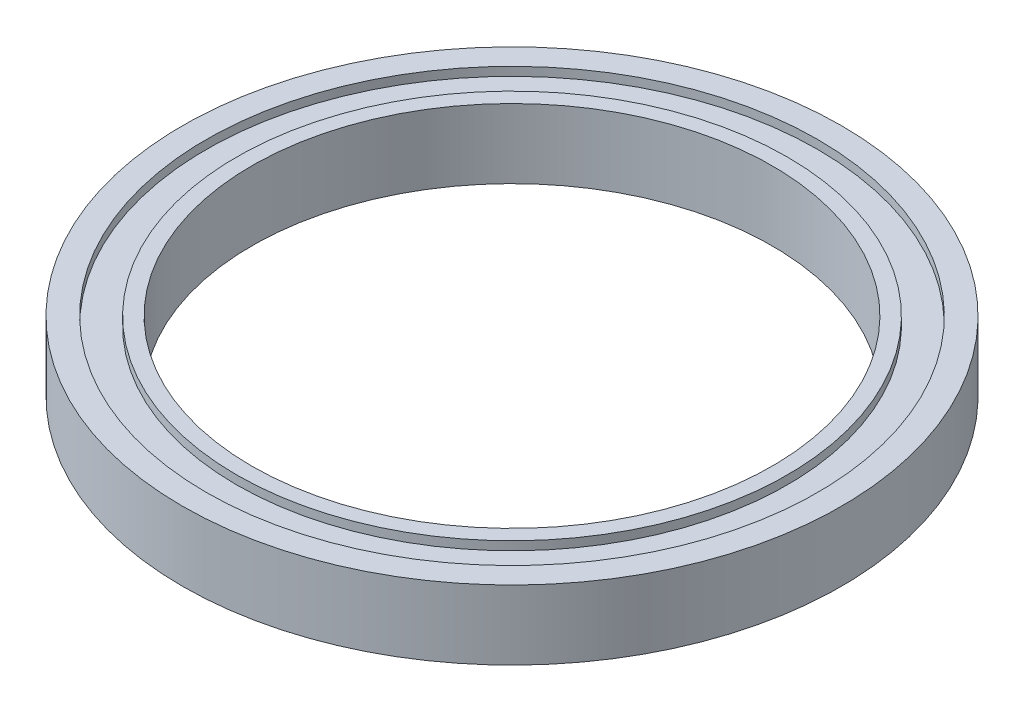
SolidWorks part; units mm, degrees
ref_plane "前视基准面" through (0, 0, 0) normal (0, 0, 1) x (1, 0, 0)
ref_plane "上视基准面" through (0, 0, 0) normal (0, 1, 0) x (1, 0, 0)
ref_plane "右视基准面" through (0, 0, 0) normal (1, 0, 0) x (0, 0, -1)
other "Configuration Table"
sketch "草图1" plane through (0, 0, 0) normal (0, 1, 0) x (1, 0, 0)
  circle A0 centre (0, 0) radius 38
  circle A1 centre (0, 0) radius 30
  dimension "D1" = 76
  dimension "D2" = 60
extrude "凸台-拉伸1" add sketch "草图1" along normal blind 8
sketch "草图2" plane through (0, 8, 0) normal (0, 1, 0) x (1, 0, 0)
  circle A0 centre (0, 0) radius 35.25
  circle A1 centre (0, 0) radius 31.75
  dimension "D1" = 63.5
  dimension "D2" = 70.5
extrude "切除-拉伸1" cut sketch "草图2" against normal blind 1
sketch "草图3" plane through (0, 0, 0) normal (0, -1, 0) x (1, 0, 0)
  circle A0 centre (0, 0) radius 35.25
  circle A1 centre (0, 0) radius 31.75
  dimension "D1" = 63.5
  dimension "D2" = 70.5
extrude "切除-拉伸2" cut sketch "草图3" against normal blind 1
